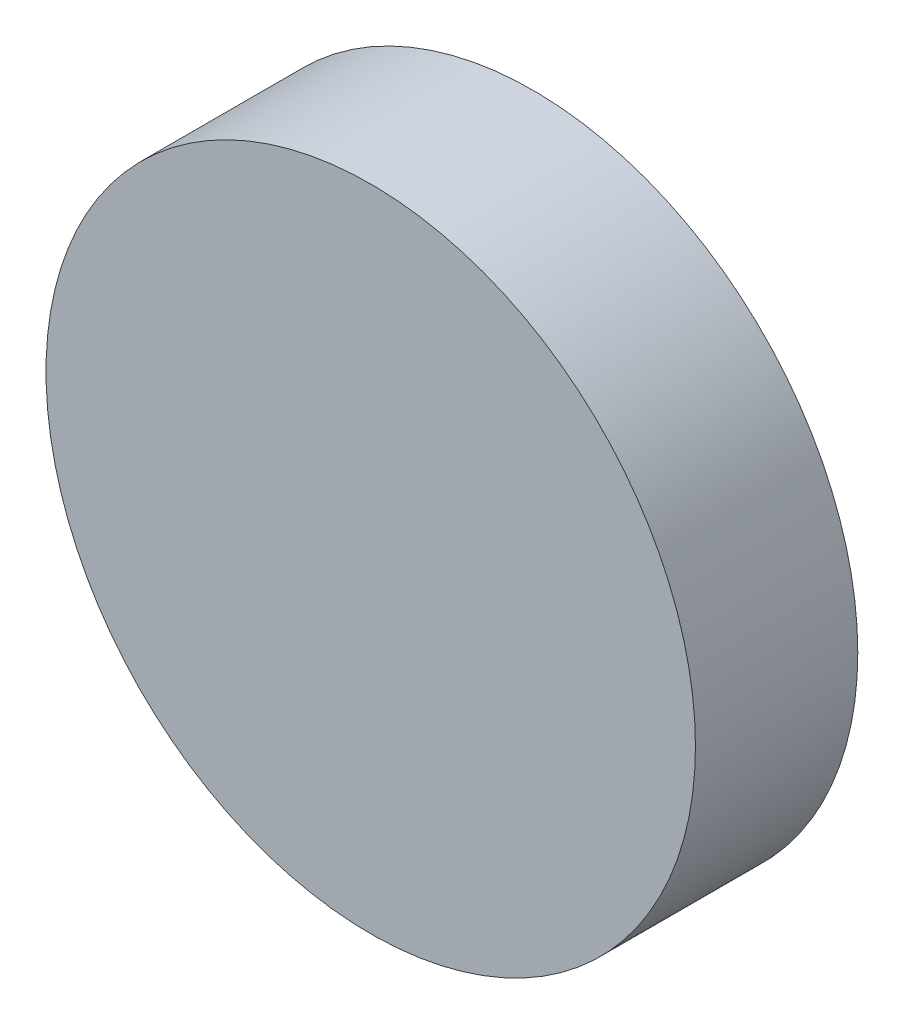
SolidWorks part; units mm, degrees
material "Nickel"
ref_plane "Front Plane" through (0, 0, 0) normal (0, 0, 1) x (1, 0, 0)
ref_plane "Top Plane" through (0, 0, 0) normal (0, 1, 0) x (1, 0, 0)
ref_plane "Right Plane" through (0, 0, 0) normal (1, 0, 0) x (0, 0, -1)
sketch "Sketch1" plane through (0, 0, 0) normal (0, 0, 1) x (1, 0, 0)
  circle A0 centre (0, 0) radius 2
  dimension "D1" = 4
extrude "Boss-Extrude1" add sketch "Sketch1" along normal mid plane 1
